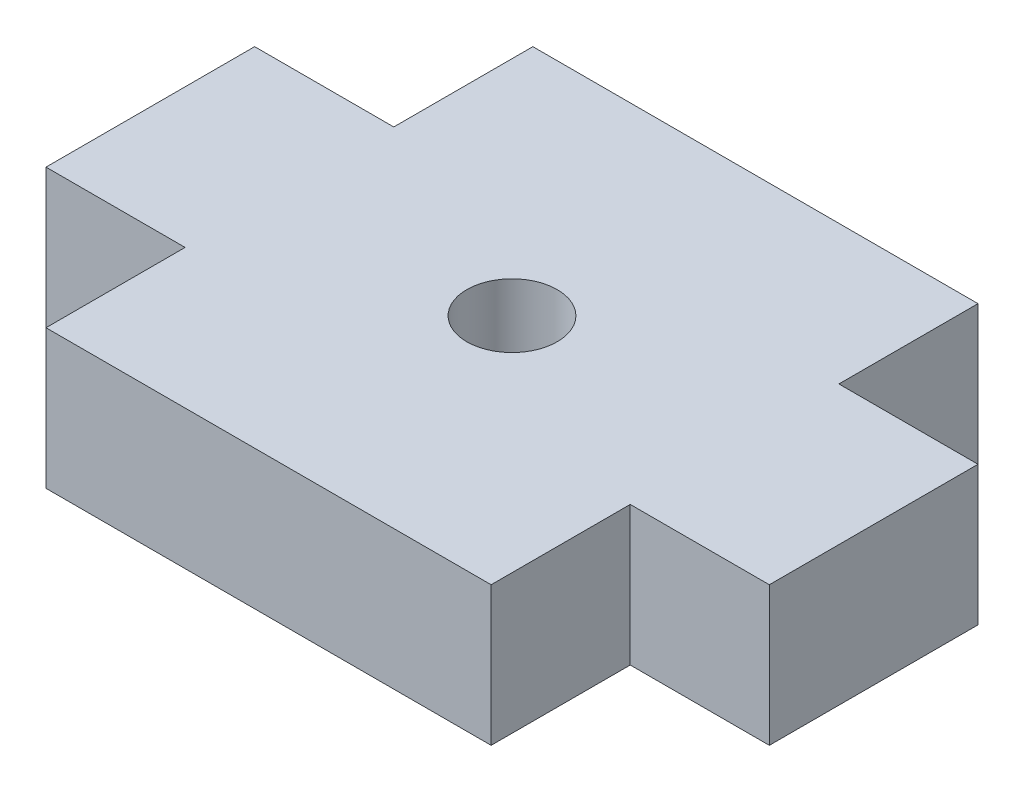
SolidWorks part; units mm, degrees
material "Acrylic (Medium-high impact)"
ref_plane "Front Plane" through (0, 0, 0) normal (0, 0, 1) x (1, 0, 0)
ref_plane "Top Plane" through (0, 0, 0) normal (0, 1, 0) x (1, 0, 0)
ref_plane "Right Plane" through (0, 0, 0) normal (1, 0, 0) x (0, 0, -1)
sketch "Sketch1" plane through (0, 0, 0) normal (0, 1, 0) x (1, 0, 0)
  line L0 (-8, 8.75) -> (8, 8.75)
  line L1 (8, 8.75) -> (8, 3.75)
  line L2 (8, 3.75) -> (13, 3.75)
  line L3 (13, 3.75) -> (13, -3.75)
  line L4 (13, 0) -> (-13, 0) construction
  line L5 (0, -8.75) -> (0, 8.75) construction
  line L6 (8, -3.75) -> (13, -3.75)
  line L7 (8, -8.75) -> (8, -3.75)
  line L8 (-8, -8.75) -> (8, -8.75)
  line L9 (-8, -8.75) -> (-8, -3.75)
  line L10 (-8, -3.75) -> (-13, -3.75)
  line L11 (-13, 3.75) -> (-13, -3.75)
  line L12 (-8, 3.75) -> (-13, 3.75)
  line L13 (-8, 8.75) -> (-8, 3.75)
  circle A0 centre (0, 0) radius 1.625
  point P12 (0, 0)
  dimension "D5" = 3.25
  dimension "D1" = 8
  dimension "D2" = 5
  dimension "D3" = 3.75
  dimension "D4" = 5
extrude "Boss-Extrude1" add sketch "Sketch1" along normal blind 5
